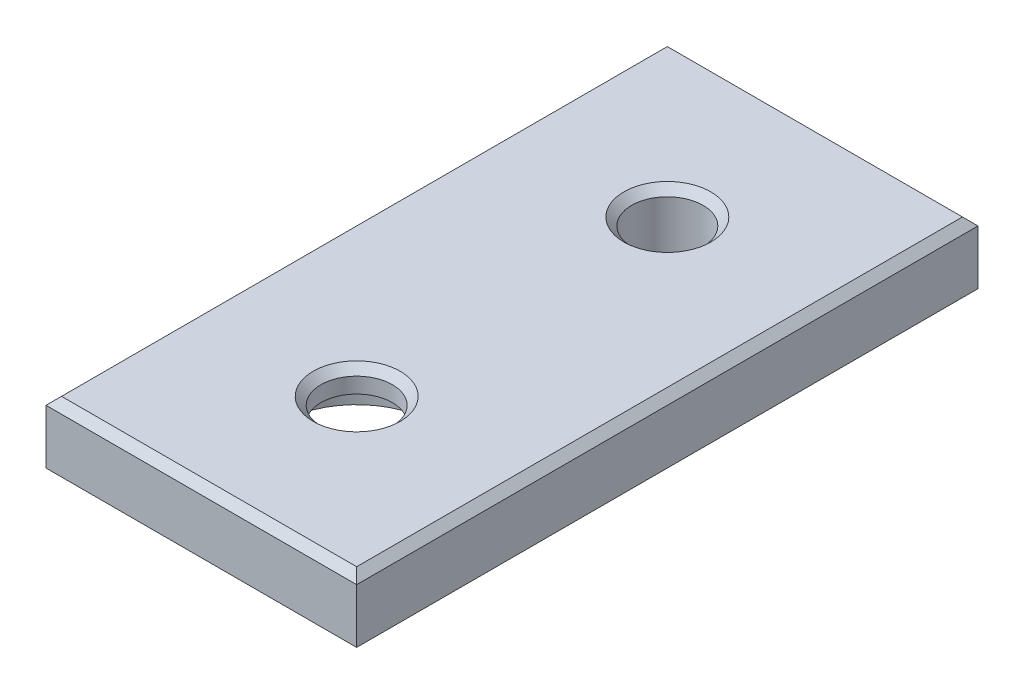
SolidWorks part; units mm, degrees
ref_plane "Plano frontal" through (0, 0, 0) normal (0, 0, 1) x (1, 0, 0)
ref_plane "Plano superior" through (0, 0, 0) normal (0, 1, 0) x (1, 0, 0)
ref_plane "Plano direito" through (0, 0, 0) normal (1, 0, 0) x (0, 0, -1)
sketch "Esboço1" plane through (0, 0, 0) normal (0, 1, 0) x (1, 0, 0)
  line L1 (-10, 20) -> (10, 20)
  line L2 (-10, 20) -> (-10, -20)
  line L3 (-10, -20) -> (10, -20)
  line L4 (10, 20) -> (10, -20)
  line L5 (-10, 20) -> (10, -20) construction
  line L6 (-10, -20) -> (10, 20) construction
  point P0 (0, 0)
  dimension "D1" = 20
  dimension "D2" = 40
extrude "Ressalto-extrusão1" add sketch "Esboço1" along normal blind 4
sketch "Esboço2" plane through (0, 4, 0) normal (0, 1, 0) x (1, 0, 0)
  line L0 (-10, 0) -> (10, 0) construction
  line L1 (-10, -20) -> (10, -20) construction
  line L2 (10, -20) -> (10, 20) construction
  line L5 (-10, 20) -> (-10, -20) construction
  line L6 (10, -20) -> (10, 20) construction
  line L7 (10, 20) -> (-10, 20) construction
  circle A0 centre (0, 10) radius 2.3
  circle A1 centre (0, -10) radius 2.3
  dimension "D1" = 4.6
  dimension "D2" = 4.6
  dimension "D3" = 10
  dimension "D4" = 10
  dimension "D5" = 10
extrude "Corte-extrusão1" cut sketch "Esboço2" against normal through all both and the other way through all
sketch "Esboço3" plane through (0, 0, 0) normal (0, -1, 0) x (1, 0, 0)
  line L0 (-10, 0) -> (10, 0) construction
  line L1 (-2.95, -7) -> (2.95, -7)
  line L2 (-2.95, -7) -> (-2.95, -1)
  line L3 (-2.95, -1) -> (2.95, -1)
  line L4 (2.95, -7) -> (2.95, -1)
  line L5 (-2.95, -7) -> (2.95, -1) construction
  line L6 (-2.95, -1) -> (2.95, -7) construction
  line L7 (-2.95, -13) -> (2.95, -13)
  line L8 (-2.95, -13) -> (-2.95, -20)
  line L9 (-2.95, -20) -> (2.95, -20)
  line L10 (2.95, -13) -> (2.95, -20)
  line L11 (-2.95, -13) -> (2.95, -20) construction
  line L12 (-2.95, -20) -> (2.95, -13) construction
  line L13 (-10, 12.95) -> (-3, 12.95)
  line L14 (-10, 12.95) -> (-10, 7.05)
  line L15 (-10, 7.05) -> (-3, 7.05)
  line L16 (-3, 12.95) -> (-3, 7.05)
  line L17 (-10, 12.95) -> (-3, 7.05) construction
  line L18 (-10, 7.05) -> (-3, 12.95) construction
  line L19 (3, 12.95) -> (10, 12.95)
  line L20 (3, 12.95) -> (3, 7.05)
  line L21 (3, 7.05) -> (10, 7.05)
  line L22 (10, 12.95) -> (10, 7.05)
  line L23 (3, 12.95) -> (10, 7.05) construction
  line L24 (3, 7.05) -> (10, 12.95) construction
  line L26 (-10, -20) -> (-10, 20) construction
  line L29 (10, 20) -> (10, -20) construction
  line L30 (10, -20) -> (-10, -20) construction
  circle A1 centre (0, -10) radius 2.3 construction
  circle A2 centre (0, 10) radius 2.3 construction
  point P0 (0, -4)
  point P5 (0, -16.5)
  point P10 (-6.5, 10)
  point P15 (6.5, 10)
  point P20 (0, 10)
  point P23 (0, -10)
  point P28 (0, -13)
  line M31 (-10, -20) -> (10, -20)
  dimension "D2" = 5.9
  dimension "D3" = 5.9
  dimension "D4" = 5.9
  dimension "D5" = 5.9
  dimension "D6" = 1
  dimension "D1" = 3
  dimension "D7" = 3
  dimension "D8" = 3
  dimension "D9" = 3
extrude "Ressalto-extrusão2" add sketch "Esboço3" along normal blind 2 contours L1 L4 L3 L2 | L10 L7 L8 M31
chamfer "Chanfro1" distance 0.5 angle 45 6 edges at (0, 4, 20) (-10, 4, 0) (0, 4, -20) (10, 4, 0) (0, 4, -7.7) (0, 4, 12.3)
sketch "Esboço4" plane through (0, 0, 0) normal (0, -1, 0) x (1, 0, 0)
  circle A0 centre (0, 10) radius 5
  dimension "D1" = 10
extrude "Corte-extrusão2" cut sketch "Esboço4" against normal blind 2.5
equation "\"D3@Esboço3\"=\"D2@Esboço3\""
equation "\"D4@Esboço3\"=\"D2@Esboço3\""
equation "\"D1@Esboço2\"=\"D2@Esboço2\""
equation "\"D8@Esboço3\"=\"D1@Esboço3\""
equation "\"D9@Esboço3\"=\"D1@Esboço3\""
